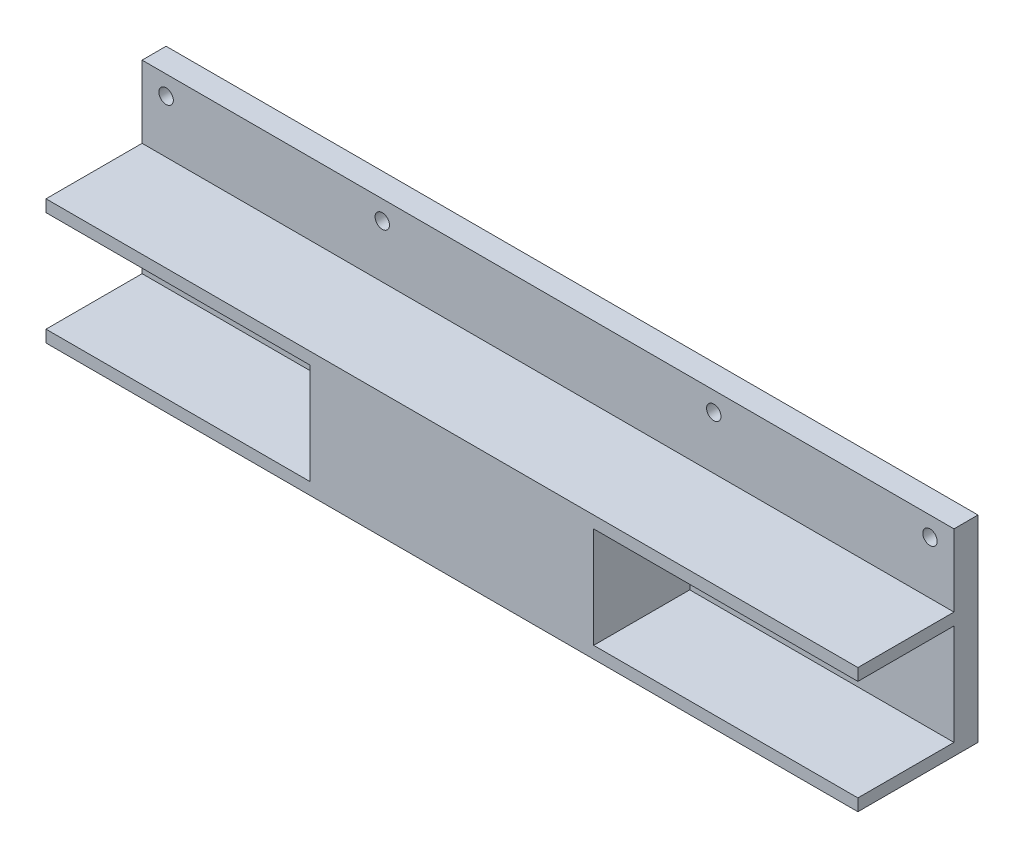
SolidWorks part; units mm, degrees
ref_plane "Спереди" through (0, 0, 0) normal (0, 0, 1) x (1, 0, 0)
ref_plane "Сверху" through (0, 0, 0) normal (0, 1, 0) x (1, 0, 0)
ref_plane "Справа" through (0, 0, 0) normal (1, 0, 0) x (0, 0, -1)
sketch "Эскиз1" plane through (0, 0, 0) normal (0, 0, 1) x (1, 0, 0)
  line L1 (-84.5, -20.5) -> (84.5, -20.5)
  line L2 (-84.5, -20.5) -> (-84.5, 20.5)
  line L3 (-84.5, 20.5) -> (84.5, 20.5)
  line L4 (84.5, -20.5) -> (84.5, 20.5)
  line L5 (0, 20.5) -> (0, -20.5) construction
  line L6 (-84.5, 0) -> (84.5, 0) construction
  point P0 (0, 0)
  dimension "D1" = 41
  dimension "D2" = 169
extrude "Бобышка-Вытянуть2" add sketch "Эскиз1" along normal blind 5
sketch "Эскиз3" plane through (0, 0, 5) normal (0, 0, 1) x (1, 0, 0)
  line L0 (84.5, -20.5) -> (84.5, 20.5) construction
  line L1 (84.5, 20.5) -> (-84.5, 20.5) construction
  line L2 (-84.5, 20.5) -> (-84.5, -20.5) construction
  circle A0 centre (79.5, 16.5) radius 1.5
  circle A1 centre (34.5, 16.5) radius 1.5
  circle A2 centre (-34.5, 16.5) radius 1.5
  circle A3 centre (-79.5, 16.5) radius 1.5
  point P14 (0, 0)
  dimension "D1" = 3
  dimension "D4" = 3
  dimension "D7" = 3
  dimension "D11" = 3
  dimension "D2" = 5
  dimension "D3" = 4
  dimension "D5" = 4
  dimension "D6" = 45
  dimension "D8" = 5
  dimension "D9" = 4
  dimension "D10" = 45
  dimension "D12" = 4
extrude "Вырез-Вытянуть1" cut sketch "Эскиз3" against normal blind 5
sketch "Эскиз4" plane through (0, 0, 5) normal (0, 0, 1) x (1, 0, 0)
  line L0 (84.5, -20.5) -> (84.5, 20.5) construction
  line L1 (-84.5, -20.5) -> (84.5, -20.5)
  line L2 (-84.5, -20.5) -> (-84.5, 5.5)
  line L3 (-84.5, 5.5) -> (84.5, 5.5)
  line L4 (84.5, -20.5) -> (84.5, 5.5)
  line L5 (0, 5.5) -> (0, -20.5) construction
  line L6 (-84.5, -7.5) -> (84.5, -7.5) construction
  point P476 (0, -7.5)
  dimension "D1" = 26
extrude "Бобышка-Вытянуть3" add sketch "Эскиз4" along normal blind 20
sketch "Эскиз5" plane through (-84.5, 0, 0) normal (-1, 0, 0) x (0, 0, 1)
  line L0 (25, 5.5) -> (25, -20.5) construction
  line L1 (25, -18) -> (5, -18)
  line L2 (25, -18) -> (25, 3)
  line L3 (25, 3) -> (5, 3)
  line L4 (5, -18) -> (5, 3)
  line L5 (15, 3) -> (15, -18) construction
  line L6 (25, -7.5) -> (5, -7.5) construction
  line L7 (25, -20.5) -> (0, -20.5) construction
  line L8 (25, 5.5) -> (5, 5.5) construction
  line L9 (0, 20.5) -> (0, -20.5) construction
  point P284 (15, -7.5)
  dimension "D1" = 2.5
  dimension "D2" = 2.5
  dimension "D3" = 5
extrude "Вырез-Вытянуть2" cut sketch "Эскиз5" against normal blind 55
sketch "Эскиз6" plane through (84.5, 0, 0) normal (1, 0, 0) x (0, 0, -1)
  line L0 (-25, -20.5) -> (-25, 5.5) construction
  line L1 (-25, 3) -> (-5, 3)
  line L2 (-25, 3) -> (-25, -18)
  line L3 (-25, -18) -> (-5, -18)
  line L4 (-5, 3) -> (-5, -18)
  line L5 (-15, -18) -> (-15, 3) construction
  line L6 (-25, -7.5) -> (-5, -7.5) construction
  line L7 (0, -20.5) -> (0, 20.5) construction
  line L8 (-25, 5.5) -> (-5, 5.5) construction
  line L9 (-25, -20.5) -> (0, -20.5) construction
  point P192 (-15, -7.5)
  dimension "D1" = 5
  dimension "D2" = 2.5
  dimension "D3" = 2.5
extrude "Вырез-Вытянуть3" cut sketch "Эскиз6" against normal blind 55
